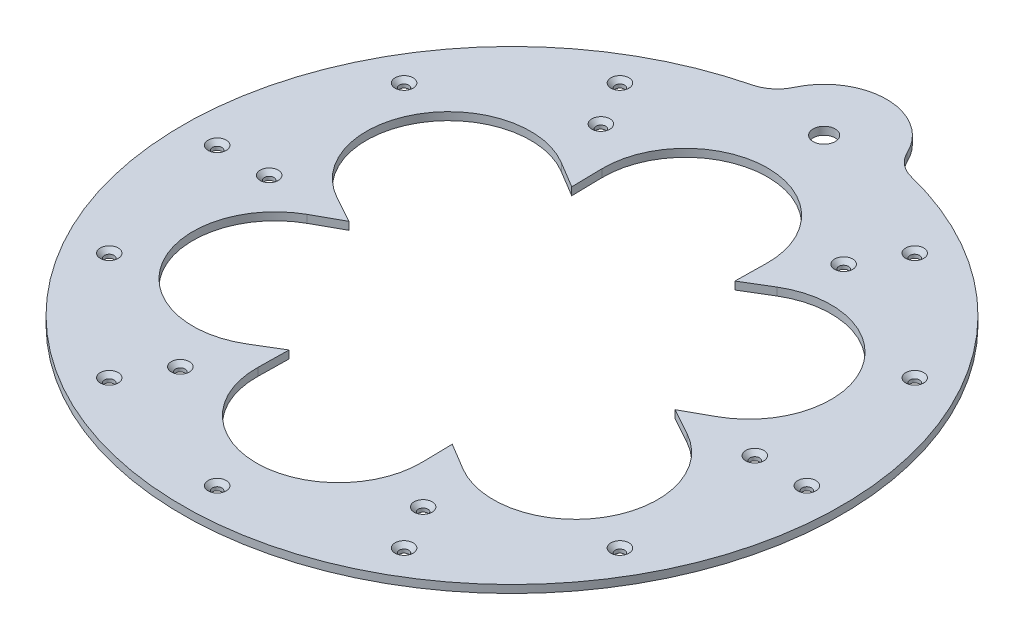
SolidWorks part; units mm, degrees
ref_plane "Front Plane" through (0, 0, 0) normal (0, 0, 1) x (1, 0, 0)
ref_plane "Top Plane" through (0, 0, 0) normal (0, 1, 0) x (1, 0, 0)
ref_plane "Right Plane" through (0, 0, 0) normal (1, 0, 0) x (0, 0, -1)
sketch "Sketch5" plane through (0, 0, 0) normal (0, 1, 0) x (1, 0, 0)
  line L25 (-47.3671, -99.136) -> (-47.0452, -81.4846)
  line L26 (47.0452, -81.4846) -> (47.3671, -99.136)
  line L28 (-47.0452, -81.4846) -> (-62.1707, -90.5891)
  line L31 (-109.5379, -8.5469) -> (-94.0903, 0)
  line L32 (-94.0903, 0) -> (-109.5379, 8.5469)
  line L35 (-62.1707, 90.5891) -> (-47.0452, 81.4846)
  line L36 (-47.0452, 81.4846) -> (-47.3671, 99.136)
  line L39 (47.3671, 99.136) -> (47.0452, 81.4846)
  line L40 (47.0452, 81.4846) -> (62.1707, 90.5891)
  line L43 (109.5379, 8.5469) -> (94.0903, 0)
  line L44 (94.0903, 0) -> (109.5379, -8.5469)
  line L47 (62.1707, -90.5891) -> (47.0452, -81.4846)
  circle A0 centre (0, 0) radius 47.9176 construction
  arc A6 (-45.8766, 184.3783) -> (45.8567, 184.3832) centre (0, 0) ccw
  circle A7 centre (0, 0) radius 29.9227 construction
  arc A14 (32.5786, 195.2947) -> (-32.5996, 195.2912) centre (-0.0097, 180) ccw
  arc A15 (-32.5996, 195.2912) -> (-45.8766, 184.3783) centre (-50.7057, 203.7865) cw
  arc A16 (32.5786, 195.2947) -> (45.8567, 184.3832) centre (50.6837, 203.792) ccw
  arc A19 (-47.3671, -99.136) -> (47.3671, -99.136) centre (0, -100) ccw
  arc A20 (-109.5379, -8.5469) -> (-62.1707, -90.5891) centre (-86.6025, -50) ccw
  arc A22 (-62.1707, 90.5891) -> (-109.5379, 8.5469) centre (-86.6025, 50) ccw
  arc A24 (47.3671, 99.136) -> (-47.3671, 99.136) centre (0, 100) ccw
  arc A26 (109.5379, 8.5469) -> (62.1707, 90.5891) centre (86.6025, 50) ccw
  arc A28 (62.1707, -90.5891) -> (109.5379, -8.5469) centre (86.6025, -50) ccw
  point P1 (0, 0)
  point P2 (0, 0)
  point P8 (0, 0)
  point P10 (0, 0)
  point P39 (-255.3022, 150.011)
  point P40 (139.5, 300)
  point P41 (0, 300)
  point P42 (-124.8076, 150)
  point P43 (-120.3076, 150)
  point P45 (-259.8076, 150)
  point P46 (135, 300)
  point P51 (0, 300)
  point P74 (0, 0)
  point P121 (0, 0)
  dimension "D2" = 20
sketch "Sketch6" plane through (0, 0, 68.1456) normal (0, -1, 0) x (1, 0, 0)
  line L0 (0, -68.1456) -> (-154.7306, -68.1456)
  circle A0 centre (0, -68.1456) radius 32.7528 construction
  circle A1 centre (0, -68.1456) radius 203.9043 construction
extrude "Boss-Extrude3" add sketch "Sketch5" against normal blind 4.5
hole_wizard "CSK for M5 Flat Head Machine Screw1" positions "Sketch8" profile "Sketch7" countersink size "M5" standard "ANSI Metric" end condition through all
sketch "Sketch8" plane through (0, 0, 68.1456) normal (0, -1, 0) x (1, 0, 0)
  line L0 (0, -68.1456) -> (-154.7306, -68.1456) construction
  point P0 (-170, -68.1456)
  dimension "D1" = 0
  dimension "D2" = 170
sketch "Sketch7" plane through (-170, 0, 0) normal (1, 0, 0) x (0, 0, 1)
  line L0 (0, 0) -> (0, 4.5)
  line L1 (0, 4.5) -> (2.75, 4.5)
  line L2 (2.75, 4.5) -> (2.75, 2.45)
  line L3 (2.75, 2.45) -> (5.2, 0)
  line L5 (5.2, 0) -> (0, 0)
  line L6 (-2.75, 2.45) -> (-5.2, 0) construction
  line L11 (0, -6.35) -> (0, 107.95) construction
  dimension "Thru Hole Dia." = 5.5
  dimension "Thru Hole Depth" = 4.5
  dimension "Near C'Sink Dia." = 10.4
  dimension "Near C'Sink Angle" = 90
pattern_circular "CirPattern1" count 12 every 30 about axis through (0, 0, 0) along (0, 1, 0) skipping 9 of "CSK for M5 Flat Head Machine Screw1"
hole_wizard "CSK for M5 Flat Head Machine Screw2" positions "Sketch10" profile "Sketch9" countersink size "M5" standard "ANSI Metric" end condition through all
sketch "Sketch10" plane through (0, 0, 68.1456) normal (0, -1, 0) x (1, 0, 0)
  line L0 (0, -68.1456) -> (-154.7306, -68.1456) construction
  point P0 (-140, -68.1456)
  dimension "D1" = 0
  dimension "D2" = 140
sketch "Sketch9" plane through (-140, 0, 0) normal (1, 0, 0) x (0, 0, 1)
  line L0 (0, 0) -> (0, 4.5)
  line L1 (0, 4.5) -> (2.75, 4.5)
  line L2 (2.75, 4.5) -> (2.75, 2.45)
  line L3 (2.75, 2.45) -> (5.2, 0)
  line L5 (5.2, 0) -> (0, 0)
  line L6 (-2.75, 2.45) -> (-5.2, 0) construction
  line L11 (0, -6.35) -> (0, 107.95) construction
  dimension "Thru Hole Dia." = 5.5
  dimension "Thru Hole Depth" = 4.5
  dimension "Near C'Sink Dia." = 10.4
  dimension "Near C'Sink Angle" = 90
pattern_circular "CirPattern2" count 6 over 360 about axis through (0, 0, 0) along (0, 1, 0) of "CSK for M5 Flat Head Machine Screw2"
ref_plane "Plane1" through (0, 0, 0) normal (0, 1, 0) x (1, 0, 0)
sketch "Sketch11" plane through (0, 0, 0) normal (0, 1, 0) x (1, 0, 0)
  circle A0 centre (-0.0097, 180) radius 6.35
extrude "Cut-Extrude1" cut sketch "Sketch11" against normal blind 10
sketch "keepThisTemplate" plane through (0, 0, 0) normal (0, 1, 0) x (1, 0, 0)
  line L0 (-86.6025, -4.4286) -> (-67.2981, -15.1094)
  line L1 (-47.1365, -72.7857) -> (-46.7342, -50.7272)
  line L2 (-47.1365, -72.7857) -> (-66.0386, -84.1634)
  line L3 (-105.9069, -15.1094) -> (-86.6025, -4.4286)
  line L4 (-47.1365, 72.7857) -> (-46.7342, 50.7272)
  line L5 (-86.6025, 4.4286) -> (-67.2981, 15.1094)
  line L6 (-86.6025, 4.4286) -> (-105.9069, 15.1094)
  line L7 (-66.0386, 84.1634) -> (-47.1365, 72.7857)
  line L8 (-39.466, -77.2143) -> (-20.564, -65.8366)
  line L9 (39.466, -77.2143) -> (20.564, -65.8366)
  line L10 (39.466, -77.2143) -> (39.8684, -99.2728)
  line L11 (-39.8684, -99.2728) -> (-39.466, -77.2143)
  line L12 (39.466, 77.2143) -> (20.564, 65.8366)
  line L13 (-39.466, 77.2143) -> (-20.564, 65.8366)
  line L14 (-39.466, 77.2143) -> (-39.8684, 99.2728)
  line L15 (39.8684, 99.2728) -> (39.466, 77.2143)
  line L16 (86.6025, 4.4286) -> (67.2981, 15.1094)
  line L17 (47.1365, 72.7857) -> (46.7342, 50.7272)
  line L18 (47.1365, 72.7857) -> (66.0386, 84.1634)
  line L19 (105.9069, 15.1094) -> (86.6025, 4.4286)
  line L20 (47.1365, -72.7857) -> (46.7342, -50.7272)
  line L21 (86.6025, -4.4286) -> (67.2981, -15.1094)
  line L22 (86.6025, -4.4286) -> (105.9069, -15.1094)
  line L23 (66.0386, -84.1634) -> (47.1365, -72.7857)
  line L24 (-46.8891, -72.9286) -> (-24.4318, -59.4109)
  line L25 (-47.3671, -99.136) -> (-46.8891, -72.9286)
  line L26 (46.8891, -72.9286) -> (47.3671, -99.136)
  line L27 (46.8891, -72.9286) -> (24.4318, -59.4109)
  line L28 (-39.7135, -77.0714) -> (-62.1707, -90.5891)
  line L29 (-39.7135, -77.0714) -> (-39.2354, -50.864)
  line L30 (-86.6025, 4.1429) -> (-63.6672, -8.5469)
  line L31 (-109.5379, -8.5469) -> (-86.6025, 4.1429)
  line L32 (-86.6025, -4.1429) -> (-109.5379, 8.5469)
  line L33 (-86.6025, -4.1429) -> (-63.6672, 8.5469)
  line L34 (-39.7135, 77.0714) -> (-39.2354, 50.864)
  line L35 (-62.1707, 90.5891) -> (-39.7135, 77.0714)
  line L36 (-46.8891, 72.9286) -> (-47.3671, 99.136)
  line L37 (-46.8891, 72.9286) -> (-24.4318, 59.4109)
  line L38 (46.8891, 72.9286) -> (24.4318, 59.4109)
  line L39 (47.3671, 99.136) -> (46.8891, 72.9286)
  line L40 (39.7135, 77.0714) -> (62.1707, 90.5891)
  line L41 (39.7135, 77.0714) -> (39.2354, 50.864)
  line L42 (86.6025, -4.1429) -> (63.6672, 8.5469)
  line L43 (109.5379, 8.5469) -> (86.6025, -4.1429)
  line L44 (86.6025, 4.1429) -> (109.5379, -8.5469)
  line L45 (86.6025, 4.1429) -> (63.6672, -8.5469)
  line L46 (39.7135, -77.0714) -> (39.2354, -50.864)
  line L47 (62.1707, -90.5891) -> (39.7135, -77.0714)
  circle A0 centre (0, 0) radius 47.9176 construction
  arc A1 (-46.7342, -50.7272) -> (-67.2981, -15.1094) centre (-86.6025, -50) ccw
  arc A2 (-105.9069, -15.1094) -> (-66.0386, -84.1634) centre (-86.6025, -50) ccw
  arc A3 (-67.2981, 15.1094) -> (-46.7342, 50.7272) centre (-86.6025, 50) ccw
  arc A4 (20.564, -65.8366) -> (-20.564, -65.8366) centre (0, -100) ccw
  arc A5 (-66.0386, 84.1634) -> (-105.9069, 15.1094) centre (-86.6025, 50) ccw
  arc A6 (-39.8684, -99.2728) -> (39.8684, -99.2728) centre (0, -100) ccw
  arc A7 (-20.564, 65.8366) -> (20.564, 65.8366) centre (0, 100) ccw
  arc A8 (39.8684, 99.2728) -> (-39.8684, 99.2728) centre (0, 100) ccw
  arc A9 (46.7342, 50.7272) -> (67.2981, 15.1094) centre (86.6025, 50) ccw
  arc A10 (105.9069, 15.1094) -> (66.0386, 84.1634) centre (86.6025, 50) ccw
  arc A11 (67.2981, -15.1094) -> (46.7342, -50.7272) centre (86.6025, -50) ccw
  arc A12 (66.0386, -84.1634) -> (105.9069, -15.1094) centre (86.6025, -50) ccw
  arc A13 (24.4318, -59.4109) -> (-24.4318, -59.4109) centre (0, -100) ccw
  arc A14 (-47.3671, -99.136) -> (47.3671, -99.136) centre (0, -100) ccw
  arc A15 (-109.5379, -8.5469) -> (-62.1707, -90.5891) centre (-86.6025, -50) ccw
  arc A16 (-39.2354, -50.864) -> (-63.6672, -8.5469) centre (-86.6025, -50) ccw
  arc A17 (-62.1707, 90.5891) -> (-109.5379, 8.5469) centre (-86.6025, 50) ccw
  arc A18 (-63.6672, 8.5469) -> (-39.2354, 50.864) centre (-86.6025, 50) ccw
  arc A19 (47.3671, 99.136) -> (-47.3671, 99.136) centre (0, 100) ccw
  arc A20 (-24.4318, 59.4109) -> (24.4318, 59.4109) centre (0, 100) ccw
  arc A21 (109.5379, 8.5469) -> (62.1707, 90.5891) centre (86.6025, 50) ccw
  arc A22 (39.2354, 50.864) -> (63.6672, 8.5469) centre (86.6025, 50) ccw
  arc A23 (62.1707, -90.5891) -> (109.5379, -8.5469) centre (86.6025, -50) ccw
  arc A24 (63.6672, -8.5469) -> (39.2354, -50.864) centre (86.6025, -50) ccw
  point P39 (-42.5504, 25.0018)
  point P40 (23.25, 50)
  point P41 (0, 50)
  point P42 (-20.8013, 25)
  point P43 (-20.0513, 25)
  point P45 (-43.3013, 25)
  point P46 (22.5, 50)
  point P51 (0, 50)
  point P61 (0, 0)
  point P110 (0, 0)
  dimension "D1" = 6
  dimension "D2" = 7.5
  dimension "D3" = 6
